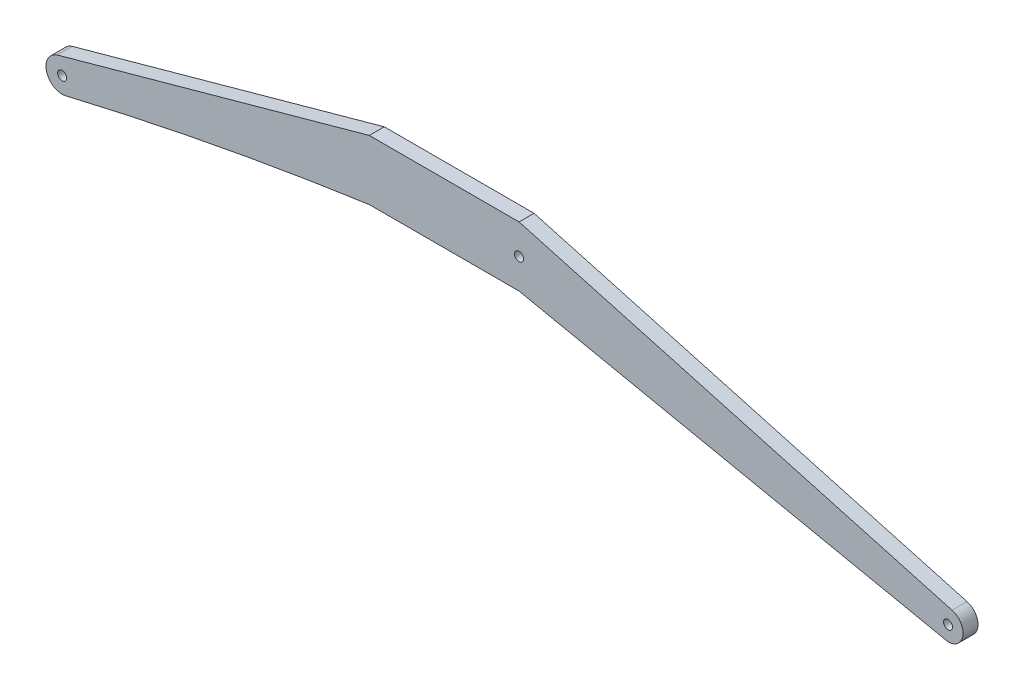
SolidWorks part; units mm, degrees
material "铸造合金钢"
ref_plane "前视基准面" through (0, 0, 0) normal (0, 0, 1) x (1, 0, 0)
ref_plane "上视基准面" through (0, 0, 0) normal (0, 1, 0) x (1, 0, 0)
ref_plane "右视基准面" through (0, 0, 0) normal (1, 0, 0) x (0, 0, -1)
sketch "草图1" plane through (0, 0, 0) normal (0, 0, 1) x (1, 0, 0)
  line L0 (-5, 1.1716) -> (5, 1.1716)
  line L1 (5, 1.1716) -> (33.9137, -6.8284)
  line L2 (0, 8.7922) -> (0, -3.304)
  line L3 (-5, 1.1716) -> (-25.8358, -4.5933)
  line L4 (-5, -2.8284) -> (5, -2.8284)
  line L6 (5, -2.8284) -> (33.647, -8.7922)
  line L7 (-25.7589, -4.5721) -> (-25.2611, -6.6704)
  circle A2 centre (33.647, -7.7922) radius 0.3
  arc A3 (33.9137, -6.8284) -> (33.2479, -8.7091) centre (33.647, -7.7922) cw
  arc A4 (-25.2611, -6.6704) -> (-5, -2.8284) centre (27.0336, -227.1045) cw
  circle A5 centre (5, -0.8284) radius 0.3
  circle A6 centre (-25.51, -5.6212) radius 0.3
  circle A7 centre (-25.51, -5.6212) radius 1.0783
  dimension "D1" = 8
  dimension "D3" = 2
extrude "凸台-拉伸1" add sketch "草图1" along normal blind 1 contours L7 A7 A6 | L3 A7 L7 A6 | A7 A4 L4 L2 L0 L3 | A3 L1 L0 L2 L4 L6 A5 A2
